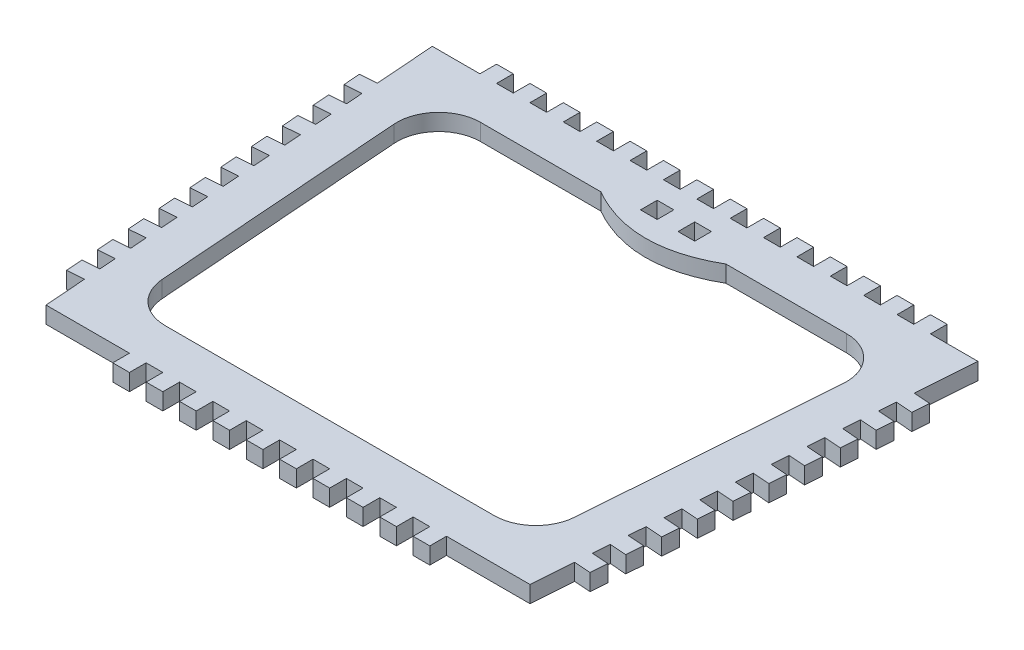
SolidWorks part; units mm, degrees
material "Cedar"
ref_plane "Front Plane" through (0, 0, 0) normal (0, 0, 1) x (1, 0, 0)
ref_plane "Top Plane" through (0, 0, 0) normal (0, 1, 0) x (1, 0, 0)
ref_plane "Right Plane" through (0, 0, 0) normal (1, 0, 0) x (0, 0, -1)
sketch "Sketch1" plane through (0, 0, 0) normal (0, 1, 0) x (1, 0, 0)
  line L0 (-65.4, 43.0243) -> (0, 43.0243)
  line L1 (65.4, 43.0243) -> (58, -56.9757)
  line L2 (58, -56.9757) -> (0, -56.9757)
  line L3 (-58, -56.9757) -> (-65.4, 43.0243)
  line L4 (0, 43.0243) -> (0, -56.9757) construction
  line L5 (0, -6.9757) -> (15.9946, -6.9757) construction
  line L48 (0, -56.9757) -> (-58, -56.9757)
  line L49 (0, 43.0243) -> (65.4, 43.0243)
  dimension "D1" = 100
  dimension "D2" = 65.4
  dimension "D3" = 58
  dimension "D14" = 65.4
  dimension "D15" = 58
extrude "Boss-Extrude1" add sketch "Sketch1" along normal blind 4
sketch "Sketch2" plane through (0, 4, 0) normal (0, 1, 0) x (1, 0, 0)
  line L0 (-65.4, 43.0243) -> (0, 43.0243) construction
  line L1 (-2, 43.0243) -> (-6, 43.0243)
  line L2 (-2, 43.0243) -> (-2, 47.0243)
  line L3 (-2, 47.0243) -> (-6, 47.0243)
  line L4 (-6, 43.0243) -> (-6, 47.0243)
  line L5 (0, 43.0243) -> (0, -56.9757) construction
  line L6 (-10, 43.0243) -> (-14, 43.0243)
  line L7 (-10, 43.0243) -> (-10, 47.0243)
  line L8 (-10, 47.0243) -> (-14, 47.0243)
  line L9 (-14, 43.0243) -> (-14, 47.0243)
  line L10 (-18, 43.0243) -> (-22, 43.0243)
  line L11 (-18, 43.0243) -> (-18, 47.0243)
  line L12 (-18, 47.0243) -> (-22, 47.0243)
  line L13 (-22, 43.0243) -> (-22, 47.0243)
  line L14 (-26, 43.0243) -> (-30, 43.0243)
  line L15 (-26, 43.0243) -> (-26, 47.0243)
  line L16 (-26, 47.0243) -> (-30, 47.0243)
  line L17 (-30, 43.0243) -> (-30, 47.0243)
  line L18 (-34, 43.0243) -> (-38, 43.0243)
  line L19 (-34, 43.0243) -> (-34, 47.0243)
  line L20 (-34, 47.0243) -> (-38, 47.0243)
  line L21 (-38, 43.0243) -> (-38, 47.0243)
  line L22 (-42, 43.0243) -> (-46, 43.0243)
  line L23 (-42, 43.0243) -> (-42, 47.0243)
  line L24 (-42, 47.0243) -> (-46, 47.0243)
  line L25 (-46, 43.0243) -> (-46, 47.0243)
  line L26 (-50, 43.0243) -> (-54, 43.0243)
  line L27 (-50, 43.0243) -> (-50, 47.0243)
  line L28 (-50, 47.0243) -> (-54, 47.0243)
  line L29 (-54, 43.0243) -> (-54, 47.0243)
  line L30 (0, 43.0243) -> (0, 11.5799) construction
  line L31 (54, 43.0243) -> (54, 47.0243)
  line L32 (50, 47.0243) -> (54, 47.0243)
  line L33 (50, 43.0243) -> (50, 47.0243)
  line L34 (50, 43.0243) -> (54, 43.0243)
  line L35 (46, 43.0243) -> (46, 47.0243)
  line L36 (42, 47.0243) -> (46, 47.0243)
  line L37 (42, 43.0243) -> (42, 47.0243)
  line L38 (42, 43.0243) -> (46, 43.0243)
  line L39 (38, 43.0243) -> (38, 47.0243)
  line L40 (34, 47.0243) -> (38, 47.0243)
  line L41 (34, 43.0243) -> (34, 47.0243)
  line L42 (34, 43.0243) -> (38, 43.0243)
  line L43 (30, 43.0243) -> (30, 47.0243)
  line L44 (26, 47.0243) -> (30, 47.0243)
  line L45 (26, 43.0243) -> (26, 47.0243)
  line L46 (26, 43.0243) -> (30, 43.0243)
  line L47 (22, 43.0243) -> (22, 47.0243)
  line L48 (18, 47.0243) -> (22, 47.0243)
  line L49 (18, 43.0243) -> (18, 47.0243)
  line L50 (18, 43.0243) -> (22, 43.0243)
  line L51 (14, 43.0243) -> (14, 47.0243)
  line L52 (10, 47.0243) -> (14, 47.0243)
  line L53 (10, 43.0243) -> (10, 47.0243)
  line L54 (10, 43.0243) -> (14, 43.0243)
  line L55 (6, 43.0243) -> (6, 47.0243)
  line L56 (2, 47.0243) -> (6, 47.0243)
  line L57 (2, 43.0243) -> (2, 47.0243)
  line L58 (2, 43.0243) -> (6, 43.0243)
  line L59 (0, -56.9757) -> (-58, -56.9757) construction
  line L60 (-6, -56.9757) -> (-2, -56.9757)
  line L61 (-6, -56.9757) -> (-6, -60.9757)
  line L62 (-6, -60.9757) -> (-2, -60.9757)
  line L63 (-2, -56.9757) -> (-2, -60.9757)
  line L64 (-14, -56.9757) -> (-10, -56.9757)
  line L65 (-14, -56.9757) -> (-14, -60.9757)
  line L66 (-14, -60.9757) -> (-10, -60.9757)
  line L67 (-10, -56.9757) -> (-10, -60.9757)
  line L68 (-22, -56.9757) -> (-18, -56.9757)
  line L69 (-22, -56.9757) -> (-22, -60.9757)
  line L70 (-22, -60.9757) -> (-18, -60.9757)
  line L71 (-18, -56.9757) -> (-18, -60.9757)
  line L72 (-30, -56.9757) -> (-26, -56.9757)
  line L73 (-30, -56.9757) -> (-30, -60.9757)
  line L74 (-30, -60.9757) -> (-26, -60.9757)
  line L75 (-26, -56.9757) -> (-26, -60.9757)
  line L76 (-38, -56.9757) -> (-34, -56.9757)
  line L77 (-38, -56.9757) -> (-38, -60.9757)
  line L78 (-38, -60.9757) -> (-34, -60.9757)
  line L79 (-34, -56.9757) -> (-34, -60.9757)
  line L80 (34, -56.9757) -> (34, -60.9757)
  line L81 (38, -60.9757) -> (34, -60.9757)
  line L82 (38, -56.9757) -> (38, -60.9757)
  line L83 (38, -56.9757) -> (34, -56.9757)
  line L84 (26, -56.9757) -> (26, -60.9757)
  line L85 (30, -60.9757) -> (26, -60.9757)
  line L86 (30, -56.9757) -> (30, -60.9757)
  line L87 (30, -56.9757) -> (26, -56.9757)
  line L88 (18, -56.9757) -> (18, -60.9757)
  line L89 (22, -60.9757) -> (18, -60.9757)
  line L90 (22, -56.9757) -> (22, -60.9757)
  line L91 (22, -56.9757) -> (18, -56.9757)
  line L92 (10, -56.9757) -> (10, -60.9757)
  line L93 (14, -60.9757) -> (10, -60.9757)
  line L94 (14, -56.9757) -> (14, -60.9757)
  line L95 (14, -56.9757) -> (10, -56.9757)
  line L96 (2, -56.9757) -> (2, -60.9757)
  line L97 (6, -60.9757) -> (2, -60.9757)
  line L98 (6, -56.9757) -> (6, -60.9757)
  line L99 (6, -56.9757) -> (2, -56.9757)
  dimension "D1" = 4
  dimension "D2" = 2
  dimension "D3" = 4
  dimension "D4" = 2
  dimension "D5" = 4
  dimension "D6" = 4
extrude "Boss-Extrude2" add sketch "Sketch2" against normal blind 4
sketch "Sketch4" plane through (0, 4, 0) normal (0, 1, 0) x (1, 0, 0)
  line L0 (-53.838, 22.2864) -> (-49.398, -37.7136)
  line L1 (-39.4253, -46.9757) -> (39.4253, -46.9757)
  line L2 (49.398, -37.7136) -> (53.838, 22.2864)
  line L3 (43.8653, 33.0243) -> (15, 33.0243)
  line L4 (65.4, 43.0243) -> (58, -56.9757) construction
  line L5 (-58, -56.9757) -> (-65.4, 43.0243) construction
  line L6 (0, -56.9757) -> (-58, -56.9757) construction
  line L7 (-65.4, 43.0243) -> (0, 43.0243) construction
  line L8 (0, 43.0243) -> (0, -56.9757) construction
  line L9 (0, 43.0243) -> (65.4, 43.0243) construction
  line L10 (-15, 33.0243) -> (-43.8653, 33.0243)
  line L11 (-6.5, 38.0243) -> (-2.5, 38.0243)
  line L17 (0, -6.9757) -> (17.2564, -6.9757) construction
  line L26 (-6.5, 38.0243) -> (-6.5, 34.0243)
  line L27 (-6.5, 34.0243) -> (-2.5, 34.0243)
  line L28 (-2.5, 38.0243) -> (-2.5, 34.0243)
  line L29 (2.5, 38.0243) -> (6.5, 38.0243)
  line L30 (2.5, 38.0243) -> (2.5, 34.0243)
  line L31 (2.5, 34.0243) -> (6.5, 34.0243)
  line L32 (6.5, 38.0243) -> (6.5, 34.0243)
  arc A0 (-49.398, -37.7136) -> (-39.4253, -46.9757) centre (-39.4253, -36.9757) ccw
  arc A1 (39.4253, -46.9757) -> (49.398, -37.7136) centre (39.4253, -36.9757) ccw
  arc A2 (53.838, 22.2864) -> (43.8653, 33.0243) centre (43.8653, 23.0243) ccw
  arc A3 (-53.838, 22.2864) -> (-43.8653, 33.0243) centre (-43.8653, 23.0243) cw
  spline S0 degree 2 poles (-15, 33.0243) (0, 24.4306) (15, 33.0243) knots 0 0 0 1 1 1
  dimension "D1" = 10
  dimension "D5" = 10
  dimension "D6" = 10
  dimension "D8" = 15
  dimension "D3" = 10
  dimension "D4" = 10
  dimension "D7" = 15
  dimension "D17" = 4
  dimension "D18" = 4
  dimension "D19" = 2.5
  dimension "D20" = 4
  dimension "D21" = 4
  dimension "D22" = 2.5
  dimension "D23" = 5
extrude "Cut-Extrude1" cut sketch "Sketch4" against normal blind 10
sketch "Sketch5" plane through (0, 4, 0) normal (0, 1, 0) x (1, 0, 0)
  line L0 (-65.4, 43.0243) -> (-58, -56.9757) construction
  line L1 (-61.7, -6.9757) -> (61.7, -6.9757) construction
  line L2 (65.4, 43.0243) -> (58, -56.9757) construction
  line L3 (0, -6.9757) -> (0, -56.9757) construction
  line L4 (-59.6236, -35.0357) -> (-63.6127, -35.3308)
  line L5 (-63.6127, -35.3308) -> (-63.3175, -39.3199)
  line L6 (-63.3175, -39.3199) -> (-59.3284, -39.0247)
  line L7 (-59.3284, -39.0247) -> (-59.6236, -35.0357)
  line L8 (-61.7, -6.9757) -> (-78.3114, -8.2049) construction
  line L9 (-59.0332, -43.0138) -> (-63.0223, -43.309)
  line L10 (-63.0223, -43.309) -> (-62.7271, -47.2981)
  line L11 (-62.7271, -47.2981) -> (-58.738, -47.0029)
  line L12 (-58.738, -47.0029) -> (-59.0332, -43.0138)
  line L13 (-60.2139, -27.0575) -> (-64.203, -27.3527)
  line L14 (-64.203, -27.3527) -> (-63.9078, -31.3418)
  line L15 (-63.9078, -31.3418) -> (-59.9188, -31.0466)
  line L16 (-59.9188, -31.0466) -> (-60.2139, -27.0575)
  line L17 (-60.8043, -19.0793) -> (-64.7934, -19.3745)
  line L18 (-64.7934, -19.3745) -> (-64.4982, -23.3636)
  line L19 (-64.4982, -23.3636) -> (-60.5091, -23.0684)
  line L20 (-60.5091, -23.0684) -> (-60.8043, -19.0793)
  line L21 (-61.3947, -11.1011) -> (-65.3838, -11.3963)
  line L22 (-65.3838, -11.3963) -> (-65.0886, -15.3854)
  line L23 (-65.0886, -15.3854) -> (-61.0995, -15.0902)
  line L24 (-61.0995, -15.0902) -> (-61.3947, -11.1011)
  line L25 (-61.9851, -3.1229) -> (-65.9742, -3.4181)
  line L26 (-65.9742, -3.4181) -> (-65.679, -7.4072)
  line L27 (-65.679, -7.4072) -> (-61.6899, -7.112)
  line L28 (-61.6899, -7.112) -> (-61.9851, -3.1229)
  line L29 (-62.5755, 4.8553) -> (-66.5646, 4.5601)
  line L30 (-66.5646, 4.5601) -> (-66.2694, 0.571)
  line L31 (-66.2694, 0.571) -> (-62.2803, 0.8662)
  line L32 (-62.2803, 0.8662) -> (-62.5755, 4.8553)
  line L33 (-63.1659, 12.8335) -> (-67.155, 12.5383)
  line L34 (-67.155, 12.5383) -> (-66.8598, 8.5492)
  line L35 (-66.8598, 8.5492) -> (-62.8707, 8.8444)
  line L36 (-62.8707, 8.8444) -> (-63.1659, 12.8335)
  line L37 (-63.7563, 20.8116) -> (-67.7454, 20.5165)
  line L38 (-67.7454, 20.5165) -> (-67.4502, 16.5274)
  line L39 (-67.4502, 16.5274) -> (-63.4611, 16.8226)
  line L40 (-63.4611, 16.8226) -> (-63.7563, 20.8116)
  line L41 (-64.3466, 28.7898) -> (-68.3357, 28.4946)
  line L42 (-68.3357, 28.4946) -> (-68.0405, 24.5055)
  line L43 (-68.0405, 24.5055) -> (-64.0515, 24.8007)
  line L44 (-64.0515, 24.8007) -> (-64.3466, 28.7898)
  line L45 (64.0515, 24.8007) -> (64.3466, 28.7898)
  line L46 (68.0405, 24.5055) -> (64.0515, 24.8007)
  line L47 (68.3357, 28.4946) -> (68.0405, 24.5055)
  line L48 (64.3466, 28.7898) -> (68.3357, 28.4946)
  line L49 (63.4611, 16.8226) -> (63.7563, 20.8116)
  line L50 (67.4502, 16.5274) -> (63.4611, 16.8226)
  line L51 (67.7454, 20.5165) -> (67.4502, 16.5274)
  line L52 (63.7563, 20.8116) -> (67.7454, 20.5165)
  line L53 (62.8707, 8.8444) -> (63.1659, 12.8335)
  line L54 (66.8598, 8.5492) -> (62.8707, 8.8444)
  line L55 (67.155, 12.5383) -> (66.8598, 8.5492)
  line L56 (63.1659, 12.8335) -> (67.155, 12.5383)
  line L57 (62.2803, 0.8662) -> (62.5755, 4.8553)
  line L58 (66.2694, 0.571) -> (62.2803, 0.8662)
  line L59 (66.5646, 4.5601) -> (66.2694, 0.571)
  line L60 (62.5755, 4.8553) -> (66.5646, 4.5601)
  line L61 (61.6899, -7.112) -> (61.9851, -3.1229)
  line L62 (65.679, -7.4072) -> (61.6899, -7.112)
  line L63 (65.9742, -3.4181) -> (65.679, -7.4072)
  line L64 (61.9851, -3.1229) -> (65.9742, -3.4181)
  line L65 (61.0995, -15.0902) -> (61.3947, -11.1011)
  line L66 (65.0886, -15.3854) -> (61.0995, -15.0902)
  line L67 (65.3838, -11.3963) -> (65.0886, -15.3854)
  line L68 (61.3947, -11.1011) -> (65.3838, -11.3963)
  line L69 (60.5091, -23.0684) -> (60.8043, -19.0793)
  line L70 (64.4982, -23.3636) -> (60.5091, -23.0684)
  line L71 (64.7934, -19.3745) -> (64.4982, -23.3636)
  line L72 (60.8043, -19.0793) -> (64.7934, -19.3745)
  line L73 (59.9188, -31.0466) -> (60.2139, -27.0575)
  line L74 (63.9078, -31.3418) -> (59.9188, -31.0466)
  line L75 (64.203, -27.3527) -> (63.9078, -31.3418)
  line L76 (60.2139, -27.0575) -> (64.203, -27.3527)
  line L77 (58.738, -47.0029) -> (59.0332, -43.0138)
  line L78 (62.7271, -47.2981) -> (58.738, -47.0029)
  line L79 (63.0223, -43.309) -> (62.7271, -47.2981)
  line L80 (59.0332, -43.0138) -> (63.0223, -43.309)
  line L81 (59.3284, -39.0247) -> (59.6236, -35.0357)
  line L82 (63.3175, -39.3199) -> (59.3284, -39.0247)
  line L83 (63.6127, -35.3308) -> (63.3175, -39.3199)
  line L84 (59.6236, -35.0357) -> (63.6127, -35.3308)
  dimension "D1" = 10
  dimension "D2" = 4
  dimension "D5" = 10
extrude "Boss-Extrude3" add sketch "Sketch5" against normal blind 4
